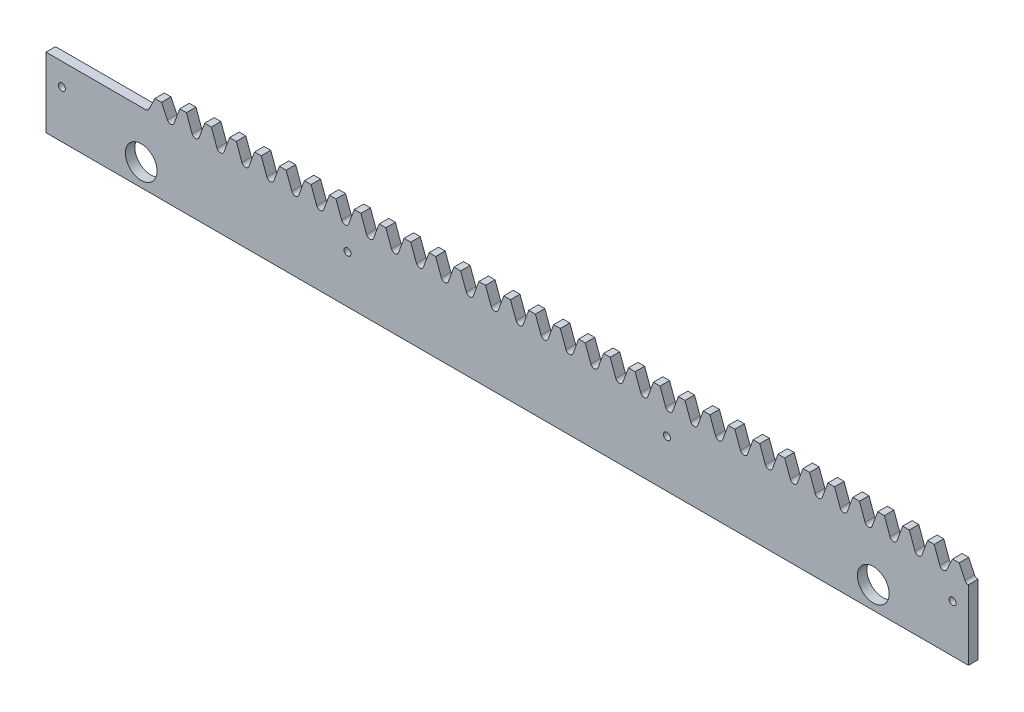
SolidWorks part; units mm, degrees
ref_plane "Plane1" through (0, 0, 0) normal (0, 0, 1) x (1, 0, 0)
ref_plane "Plane2" through (0, 0, 0) normal (0, 1, 0) x (1, 0, 0)
ref_plane "Plane3" through (0, 0, 0) normal (1, 0, 0) x (0, 0, -1)
sketch "Esquisse1" plane through (0, 0, 0) normal (0, 0, 1) x (1, 0, 0)
  line L0 (-11.781, 22) -> (19.635, 22)
  line L1 (23.5619, 29.1362) -> (23.5619, 19.2192) construction
  line L2 (-16.2297, 22) -> (24.6155, 22) construction
  line L3 (18.2522, 26.5) -> (283.3605, 26.5) construction
  line L4 (22.5084, 28.8854) -> (22.5084, 23.1798) construction
  line L5 (22.5084, 26.5) -> (20.6365, 22.5562)
  line L6 (24.6155, 26.5) -> (26.4874, 22.5562)
  line L8 (22.5084, 26.5) -> (24.6155, 26.5)
  line L10 (275.9429, 26.742) -> (275.9429, 19.9201) construction
  line L11 (273.8358, 26.742) -> (273.8358, 19.9201) construction
  line L12 (273.8358, 26.5) -> (272.0069, 22.6314)
  line L13 (275.9429, 26.5) -> (277.7718, 22.6314)
  line L14 (273.8358, 26.5) -> (275.9429, 26.5)
  line L20 (28.5976, 22.7763) -> (30.3624, 27.625)
  line L21 (30.3624, 27.625) -> (32.4695, 27.625)
  line L22 (34.2343, 22.7763) -> (32.4695, 27.625)
  line L23 (36.4515, 22.7763) -> (38.2163, 27.625)
  line L24 (38.2163, 27.625) -> (40.3235, 27.625)
  line L25 (42.0883, 22.7763) -> (40.3235, 27.625)
  line L26 (44.3055, 22.7763) -> (46.0703, 27.625)
  line L27 (46.0703, 27.625) -> (48.1775, 27.625)
  line L28 (49.9423, 22.7763) -> (48.1775, 27.625)
  line L29 (52.1595, 22.7763) -> (53.9243, 27.625)
  line L30 (53.9243, 27.625) -> (56.0314, 27.625)
  line L31 (57.7962, 22.7763) -> (56.0314, 27.625)
  line L32 (60.0135, 22.7763) -> (61.7783, 27.625)
  line L33 (61.7783, 27.625) -> (63.8854, 27.625)
  line L34 (65.6502, 22.7763) -> (63.8854, 27.625)
  line L35 (67.8675, 22.7763) -> (69.6323, 27.625)
  line L36 (69.6323, 27.625) -> (71.7394, 27.625)
  line L37 (73.5042, 22.7763) -> (71.7394, 27.625)
  line L38 (75.7215, 22.7763) -> (77.4862, 27.625)
  line L39 (77.4862, 27.625) -> (79.5934, 27.625)
  line L40 (81.3582, 22.7763) -> (79.5934, 27.625)
  line L41 (83.5754, 22.7763) -> (85.3402, 27.625)
  line L42 (85.3402, 27.625) -> (87.4474, 27.625)
  line L43 (89.2122, 22.7763) -> (87.4474, 27.625)
  line L44 (91.4294, 22.7763) -> (93.1942, 27.625)
  line L45 (93.1942, 27.625) -> (95.3013, 27.625)
  line L46 (97.0661, 22.7763) -> (95.3013, 27.625)
  line L47 (99.2834, 22.7763) -> (101.0482, 27.625)
  line L48 (101.0482, 27.625) -> (103.1553, 27.625)
  line L49 (104.9201, 22.7763) -> (103.1553, 27.625)
  line L50 (107.1374, 22.7763) -> (108.9022, 27.625)
  line L51 (108.9022, 27.625) -> (111.0093, 27.625)
  line L52 (112.7741, 22.7763) -> (111.0093, 27.625)
  line L53 (114.9914, 22.7763) -> (116.7562, 27.625)
  line L54 (116.7562, 27.625) -> (118.8633, 27.625)
  line L55 (120.6281, 22.7763) -> (118.8633, 27.625)
  line L56 (122.8453, 22.7763) -> (124.6101, 27.625)
  line L57 (124.6101, 27.625) -> (126.7173, 27.625)
  line L58 (128.4821, 22.7763) -> (126.7173, 27.625)
  line L59 (130.6993, 22.7763) -> (132.4641, 27.625)
  line L60 (132.4641, 27.625) -> (134.5713, 27.625)
  line L61 (136.3361, 22.7763) -> (134.5713, 27.625)
  line L62 (138.5533, 22.7763) -> (140.3181, 27.625)
  line L63 (140.3181, 27.625) -> (142.4252, 27.625)
  line L64 (144.19, 22.7763) -> (142.4252, 27.625)
  line L65 (146.4073, 22.7763) -> (148.1721, 27.625)
  line L66 (148.1721, 27.625) -> (150.2792, 27.625)
  line L67 (152.044, 22.7763) -> (150.2792, 27.625)
  line L68 (154.2613, 22.7763) -> (156.0261, 27.625)
  line L69 (156.0261, 27.625) -> (158.1332, 27.625)
  line L70 (159.898, 22.7763) -> (158.1332, 27.625)
  line L71 (162.1153, 22.7763) -> (163.88, 27.625)
  line L72 (163.88, 27.625) -> (165.9872, 27.625)
  line L73 (167.752, 22.7763) -> (165.9872, 27.625)
  line L74 (169.9692, 22.7763) -> (171.734, 27.625)
  line L75 (171.734, 27.625) -> (173.8412, 27.625)
  line L76 (175.606, 22.7763) -> (173.8412, 27.625)
  line L77 (177.8232, 22.7763) -> (179.588, 27.625)
  line L78 (179.588, 27.625) -> (181.6951, 27.625)
  line L79 (183.4599, 22.7763) -> (181.6951, 27.625)
  line L80 (185.6772, 22.7763) -> (187.442, 27.625)
  line L81 (187.442, 27.625) -> (189.5491, 27.625)
  line L82 (191.3139, 22.7763) -> (189.5491, 27.625)
  line L83 (193.5312, 22.7763) -> (195.296, 27.625)
  line L84 (195.296, 27.625) -> (197.4031, 27.625)
  line L85 (199.1679, 22.7763) -> (197.4031, 27.625)
  line L86 (201.3852, 22.7763) -> (203.15, 27.625)
  line L87 (203.15, 27.625) -> (205.2571, 27.625)
  line L88 (207.0219, 22.7763) -> (205.2571, 27.625)
  line L89 (209.2391, 22.7763) -> (211.0039, 27.625)
  line L90 (211.0039, 27.625) -> (213.1111, 27.625)
  line L91 (214.8759, 22.7763) -> (213.1111, 27.625)
  line L92 (217.0931, 22.7763) -> (218.8579, 27.625)
  line L93 (218.8579, 27.625) -> (220.9651, 27.625)
  line L94 (222.7298, 22.7763) -> (220.9651, 27.625)
  line L95 (224.9471, 22.7763) -> (226.7119, 27.625)
  line L96 (226.7119, 27.625) -> (228.819, 27.625)
  line L97 (230.5838, 22.7763) -> (228.819, 27.625)
  line L98 (232.8011, 22.7763) -> (234.5659, 27.625)
  line L99 (234.5659, 27.625) -> (236.673, 27.625)
  line L100 (238.4378, 22.7763) -> (236.673, 27.625)
  line L101 (240.6551, 22.7763) -> (242.4199, 27.625)
  line L102 (242.4199, 27.625) -> (244.527, 27.625)
  line L103 (246.2918, 22.7763) -> (244.527, 27.625)
  line L104 (248.509, 22.7763) -> (250.2738, 27.625)
  line L105 (250.2738, 27.625) -> (252.381, 27.625)
  line L106 (254.1458, 22.7763) -> (252.381, 27.625)
  line L107 (256.363, 22.7763) -> (258.1278, 27.625)
  line L108 (258.1278, 27.625) -> (260.235, 27.625)
  line L109 (261.9998, 22.7763) -> (260.235, 27.625)
  line L110 (264.217, 22.7763) -> (265.9818, 27.625)
  line L111 (265.9818, 27.625) -> (268.0889, 27.625)
  line L112 (269.8537, 22.7763) -> (268.0889, 27.625)
  line L114 (19.635, 37.0607) -> (19.635, -15.8181) construction
  line L115 (283.3605, 22) -> (228.0591, 22) construction
  line L118 (-11.781, 22) -> (-11.781, 0)
  line L121 (278.8759, 22.0015) -> (278.8759, 0)
  line L131 (278.8759, 0) -> (-11.781, 0)
  line L132 (133.5177, 28.2837) -> (133.5177, 9.5143) construction
  line L133 (130.5371, 22) -> (141.4123, 22) construction
  line L149 (273.8358, 27.625) -> (275.9429, 27.625) [skipped]
  line L150 (277.7077, 22.7763) -> (275.9429, 27.625) [skipped]
  line L151 (272.071, 22.7763) -> (273.8358, 27.625) [skipped]
  circle A0 centre (183.8759, 15) radius 1.1
  circle A1 centre (83.219, 15) radius 1.1
  arc A7 (19.635, 22) -> (20.6365, 22.5562) centre (19.635, 23.1798) ccw
  arc A8 (27.4889, 22) -> (26.4874, 22.5562) centre (27.4889, 23.1798) cw
  arc A9 (27.4889, 22) -> (28.5976, 22.7763) centre (27.4889, 23.1798) ccw
  arc A10 (35.3429, 22) -> (34.2343, 22.7763) centre (35.3429, 23.1798) cw
  arc A11 (35.3429, 22) -> (36.4515, 22.7763) centre (35.3429, 23.1798) ccw
  arc A12 (43.1969, 22) -> (42.0883, 22.7763) centre (43.1969, 23.1798) cw
  arc A13 (43.1969, 22) -> (44.3055, 22.7763) centre (43.1969, 23.1798) ccw
  arc A14 (51.0509, 22) -> (49.9423, 22.7763) centre (51.0509, 23.1798) cw
  arc A15 (51.0509, 22) -> (52.1595, 22.7763) centre (51.0509, 23.1798) ccw
  arc A16 (58.9049, 22) -> (57.7962, 22.7763) centre (58.9049, 23.1798) cw
  arc A17 (58.9049, 22) -> (60.0135, 22.7763) centre (58.9049, 23.1798) ccw
  arc A18 (66.7588, 22) -> (65.6502, 22.7763) centre (66.7588, 23.1798) cw
  arc A19 (66.7588, 22) -> (67.8675, 22.7763) centre (66.7588, 23.1798) ccw
  arc A20 (74.6128, 22) -> (73.5042, 22.7763) centre (74.6128, 23.1798) cw
  arc A21 (74.6128, 22) -> (75.7215, 22.7763) centre (74.6128, 23.1798) ccw
  arc A22 (82.4668, 22) -> (81.3582, 22.7763) centre (82.4668, 23.1798) cw
  arc A23 (82.4668, 22) -> (83.5754, 22.7763) centre (82.4668, 23.1798) ccw
  arc A24 (90.3208, 22) -> (89.2122, 22.7763) centre (90.3208, 23.1798) cw
  arc A25 (90.3208, 22) -> (91.4294, 22.7763) centre (90.3208, 23.1798) ccw
  arc A26 (98.1748, 22) -> (97.0661, 22.7763) centre (98.1748, 23.1798) cw
  arc A27 (98.1748, 22) -> (99.2834, 22.7763) centre (98.1748, 23.1798) ccw
  arc A28 (106.0288, 22) -> (104.9201, 22.7763) centre (106.0288, 23.1798) cw
  arc A29 (106.0288, 22) -> (107.1374, 22.7763) centre (106.0288, 23.1798) ccw
  arc A30 (113.8827, 22) -> (112.7741, 22.7763) centre (113.8827, 23.1798) cw
  arc A31 (113.8827, 22) -> (114.9914, 22.7763) centre (113.8827, 23.1798) ccw
  arc A32 (121.7367, 22) -> (120.6281, 22.7763) centre (121.7367, 23.1798) cw
  arc A33 (121.7367, 22) -> (122.8453, 22.7763) centre (121.7367, 23.1798) ccw
  arc A34 (129.5907, 22) -> (128.4821, 22.7763) centre (129.5907, 23.1798) cw
  arc A35 (129.5907, 22) -> (130.6993, 22.7763) centre (129.5907, 23.1798) ccw
  arc A36 (137.4447, 22) -> (136.3361, 22.7763) centre (137.4447, 23.1798) cw
  arc A37 (137.4447, 22) -> (138.5533, 22.7763) centre (137.4447, 23.1798) ccw
  arc A38 (145.2987, 22) -> (144.19, 22.7763) centre (145.2987, 23.1798) cw
  arc A39 (145.2987, 22) -> (146.4073, 22.7763) centre (145.2987, 23.1798) ccw
  arc A40 (153.1526, 22) -> (152.044, 22.7763) centre (153.1526, 23.1798) cw
  arc A41 (153.1526, 22) -> (154.2613, 22.7763) centre (153.1526, 23.1798) ccw
  arc A42 (161.0066, 22) -> (159.898, 22.7763) centre (161.0066, 23.1798) cw
  arc A43 (161.0066, 22) -> (162.1153, 22.7763) centre (161.0066, 23.1798) ccw
  arc A44 (168.8606, 22) -> (167.752, 22.7763) centre (168.8606, 23.1798) cw
  arc A45 (168.8606, 22) -> (169.9692, 22.7763) centre (168.8606, 23.1798) ccw
  arc A46 (176.7146, 22) -> (175.606, 22.7763) centre (176.7146, 23.1798) cw
  arc A47 (176.7146, 22) -> (177.8232, 22.7763) centre (176.7146, 23.1798) ccw
  arc A48 (184.5686, 22) -> (183.4599, 22.7763) centre (184.5686, 23.1798) cw
  arc A49 (184.5686, 22) -> (185.6772, 22.7763) centre (184.5686, 23.1798) ccw
  arc A50 (192.4226, 22) -> (191.3139, 22.7763) centre (192.4226, 23.1798) cw
  arc A51 (192.4226, 22) -> (193.5312, 22.7763) centre (192.4226, 23.1798) ccw
  arc A52 (200.2765, 22) -> (199.1679, 22.7763) centre (200.2765, 23.1798) cw
  arc A53 (200.2765, 22) -> (201.3852, 22.7763) centre (200.2765, 23.1798) ccw
  arc A54 (208.1305, 22) -> (207.0219, 22.7763) centre (208.1305, 23.1798) cw
  arc A55 (208.1305, 22) -> (209.2391, 22.7763) centre (208.1305, 23.1798) ccw
  arc A56 (215.9845, 22) -> (214.8759, 22.7763) centre (215.9845, 23.1798) cw
  arc A57 (215.9845, 22) -> (217.0931, 22.7763) centre (215.9845, 23.1798) ccw
  arc A58 (223.8385, 22) -> (222.7298, 22.7763) centre (223.8385, 23.1798) cw
  arc A59 (223.8385, 22) -> (224.9471, 22.7763) centre (223.8385, 23.1798) ccw
  arc A60 (231.6925, 22) -> (230.5838, 22.7763) centre (231.6925, 23.1798) cw
  arc A61 (231.6925, 22) -> (232.8011, 22.7763) centre (231.6925, 23.1798) ccw
  arc A62 (239.5464, 22) -> (238.4378, 22.7763) centre (239.5464, 23.1798) cw
  arc A63 (239.5464, 22) -> (240.6551, 22.7763) centre (239.5464, 23.1798) ccw
  arc A64 (247.4004, 22) -> (246.2918, 22.7763) centre (247.4004, 23.1798) cw
  arc A65 (247.4004, 22) -> (248.509, 22.7763) centre (247.4004, 23.1798) ccw
  arc A66 (255.2544, 22) -> (254.1458, 22.7763) centre (255.2544, 23.1798) cw
  arc A67 (255.2544, 22) -> (256.363, 22.7763) centre (255.2544, 23.1798) ccw
  arc A68 (263.1084, 22) -> (261.9998, 22.7763) centre (263.1084, 23.1798) cw
  arc A69 (263.1084, 22) -> (264.217, 22.7763) centre (263.1084, 23.1798) ccw
  arc A70 (270.9624, 22) -> (269.8537, 22.7763) centre (270.9624, 23.1798) cw
  arc A72 (270.9624, 22) -> (272.0069, 22.6314) centre (270.9624, 23.1798) ccw
  arc A79 (278.8759, 22.0015) -> (277.7718, 22.6314) centre (278.8163, 23.1798) cw
  circle A81 centre (-6.781, 15) radius 1.1
  circle A82 centre (273.8759, 15) radius 1.1
  dimension "D2" = 4.5
  dimension "D3" = 2.2
  dimension "D4" = 2.2
  dimension "D5" = 2.2
  dimension "D6" = 2.2
  dimension "D8" = 290.6568
  dimension "D9" = 90
  dimension "D10" = 5
  dimension "D11" = 90
  dimension "D7" = 5
  dimension "D12" = 100.6568
  dimension "D13" = 15
  dimension "D14" = 11.781
extrude "Extrusion1" add sketch "Esquisse1" along normal blind 3
sketch "Esquisse4" plane through (0, 0, 3) normal (0, 0, 1) x (1, 0, 0)
  line L0 (278.8759, 0) -> (-11.781, 0) construction
  line L1 (278.8759, 22.0015) -> (278.8759, 0) construction
  line L2 (-11.781, 22) -> (-11.781, 0) construction
  circle A0 centre (18.219, 7) radius 5
  circle A2 centre (248.8759, 7) radius 5
  dimension "D1" = 10
  dimension "D2" = 7
  dimension "D3" = 30
  dimension "D4" = 30
extrude "Enlèv. mat.-Extru.2" cut sketch "Esquisse4" against normal through all
